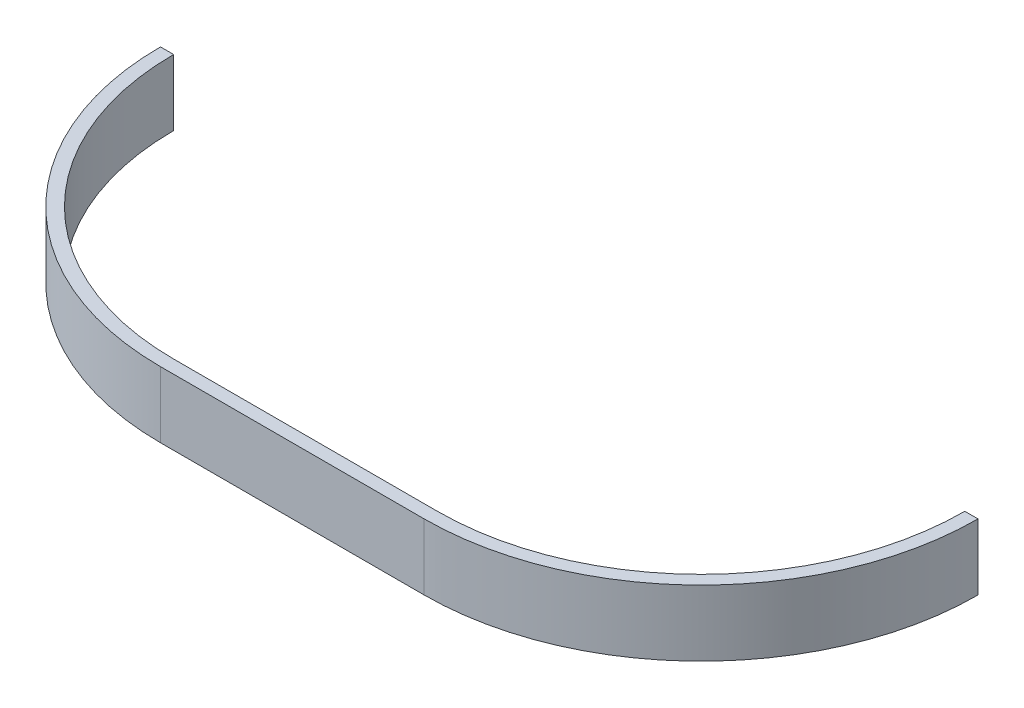
SolidWorks part; units mm, degrees
ref_plane "Front" through (0, 0, 0) normal (0, 0, 1) x (1, 0, 0)
ref_plane "Top" through (0, 0, 0) normal (0, 1, 0) x (1, 0, 0)
ref_plane "Right" through (0, 0, 0) normal (1, 0, 0) x (0, 0, -1)
sketch "草图1" plane through (0, 0, 0) normal (0, 1, 0) x (1, 0, 0)
  line L1 (120, 0) -> (124, 0)
  line L3 (-40, -84) -> (40, -84)
  line L6 (-40, -80) -> (40, -80)
  line L7 (-124, 0) -> (-120, 0)
  arc A0 (-124, 0) -> (-40, -84) centre (-40, 0) ccw
  arc A1 (40, -84) -> (124, 0) centre (40, 0) ccw
  arc A2 (-120, 0) -> (-40, -80) centre (-40, 0) ccw
  arc A3 (40, -80) -> (120, 0) centre (40, 0) ccw
  point P5 (0, 0)
  point P11 (0, 0)
extrude "凸台-拉伸1" add sketch "草图1" along normal blind 20
